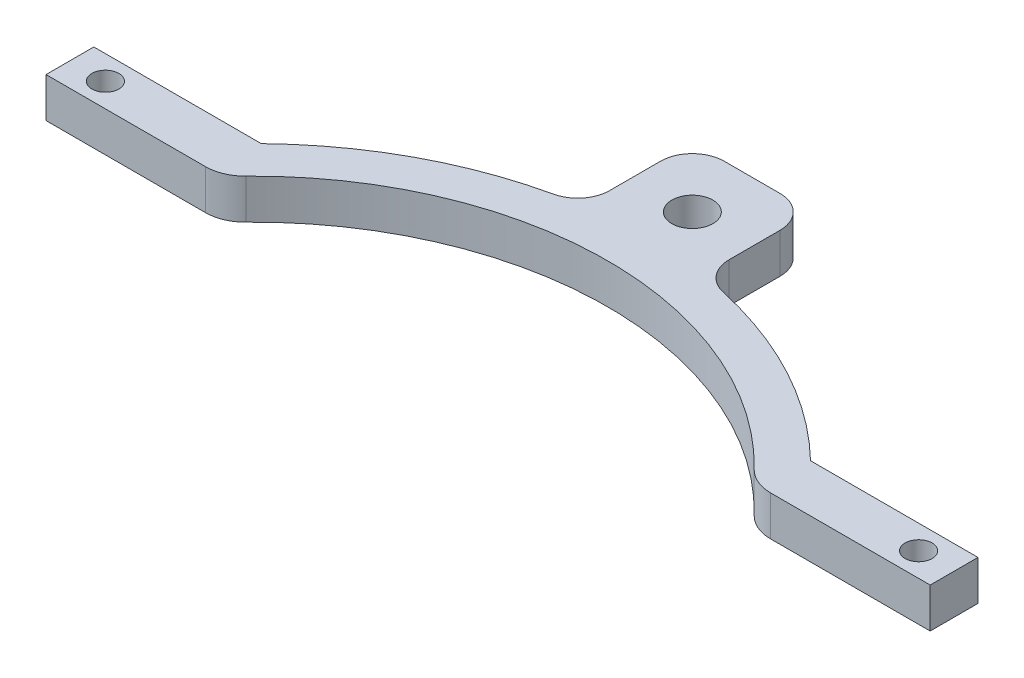
SolidWorks part; units mm, degrees
other "Markup1"
sketch "Sketch15" plane through (-79.375, 6.35, -79.375) normal (0, 1, 0) x (1, 0, 0)
other "Markup2"
sketch "Sketch16" plane through (-79.375, 6.35, -79.375) normal (0, 1, 0) x (1, 0, 0)
material "6061-T6 (SS)"
ref_plane "Front Plane" through (0, 0, 0) normal (0, 0, 1) x (1, 0, 0)
ref_plane "Top Plane" through (0, 0, 0) normal (0, 1, 0) x (1, 0, 0)
ref_plane "Right Plane" through (0, 0, 0) normal (1, 0, 0) x (0, 0, -1)
sketch "Sketch1" plane through (0, 0, 0) normal (0, 1, 0) x (1, 0, 0)
  circle A0 centre (0, 0) radius 56.3626
  circle A1 centre (0, 0) radius 62.7062
  dimension "D1" = 112.7252
  dimension "D2" = 125.4125
extrude "Boss-Extrude1" add sketch "Sketch1" along normal blind 6.35
sketch "Sketch5" plane through (0, 6.35, 0) normal (0, 1, 0) x (1, 0, 0)
  line L0 (0, 0) -> (0, 60.5427) construction
  line L1 (-9.525, 60.5427) -> (9.525, 60.5427)
  line L2 (-9.525, 60.5427) -> (-9.525, 79.375)
  line L5 (-9.525, 79.375) -> (9.525, 79.375)
  line L6 (9.525, 79.375) -> (9.525, 60.5427)
  dimension "D2" = 19.05
  dimension "D3" = 79.375
extrude "Boss-Extrude2" add sketch "Sketch5" against normal blind 6.35
fillet "Fillet1" radius 5.08 4 edges at (-9.525, 3.175, -61.9786) (9.525, 3.175, -61.9786) (-9.525, 3.175, -79.375) (9.525, 3.175, -79.375)
sketch "Sketch11" plane through (0, 0, 0) normal (0, -1, 0) x (1, 0, 0)
  circle A0 centre (0, -69.85) radius 3.2639
  dimension "D1" = 6.5278
  dimension "D2" = 69.85
extrude "Cut-Extrude2" cut sketch "Sketch11" against normal through all
sketch "Sketch17" plane through (0, 6.35, 0) normal (0, 1, 0) x (1, 0, 0)
  line L0 (0, 56.3626) -> (0, -44.1686) construction
  line L1 (-84.8924, 37.3126) -> (84.8924, 37.3126)
  line L2 (-84.8924, 37.3126) -> (-84.8924, -79.6753)
  line L3 (-84.8924, -79.6753) -> (84.8924, -79.6753)
  line L4 (84.8924, -79.6753) -> (84.8924, 37.3126)
  circle A0 centre (0, 0) radius 56.3626 construction
  point P9 (0, 23.6275)
  dimension "D1" = 19.05
extrude "Cut-Extrude3" cut sketch "Sketch17" against normal through all
fillet "Fillet2" radius 6.35 2 edges at (42.2435, 3.175, -37.3126) (-42.2435, 3.175, -37.3126)
sketch "Sketch18" plane through (0, 6.35, 0) normal (0, 1, 0) x (1, 0, 0)
  line L0 (-50.3969, 37.3126) -> (-70.4161, 37.3126)
  line L1 (-70.4161, 37.3126) -> (-70.4161, 44.9326)
  line L2 (-70.4161, 44.9326) -> (-43.7394, 44.9326)
  line L3 (-50.3969, 37.3126) -> (-43.7394, 44.9326)
  line L5 (0, -3.4925) -> (0, 3.4925) construction
  line L6 (50.3969, 37.3126) -> (43.7394, 44.9326)
  line L7 (70.4161, 44.9326) -> (43.7394, 44.9326)
  line L8 (70.4161, 37.3126) -> (70.4161, 44.9326)
  line L9 (50.3969, 37.3126) -> (70.4161, 37.3126)
  line L10 (-70.4161, 41.1226) -> (-64.77, 41.1226) construction
  arc A0 (-13.5105, 61.2335) -> (-50.3969, 37.3126) centre (0, 0) ccw construction
  circle A1 centre (-64.77, 41.1226) radius 2.1527
  circle A2 centre (64.77, 41.1226) radius 2.1527
  dimension "D3" = 4.3053
  dimension "D1" = 25.4
  dimension "D2" = 7.62
  dimension "D4" = 64.77
extrude "Boss-Extrude4" add sketch "Sketch18" against normal blind 6.35
